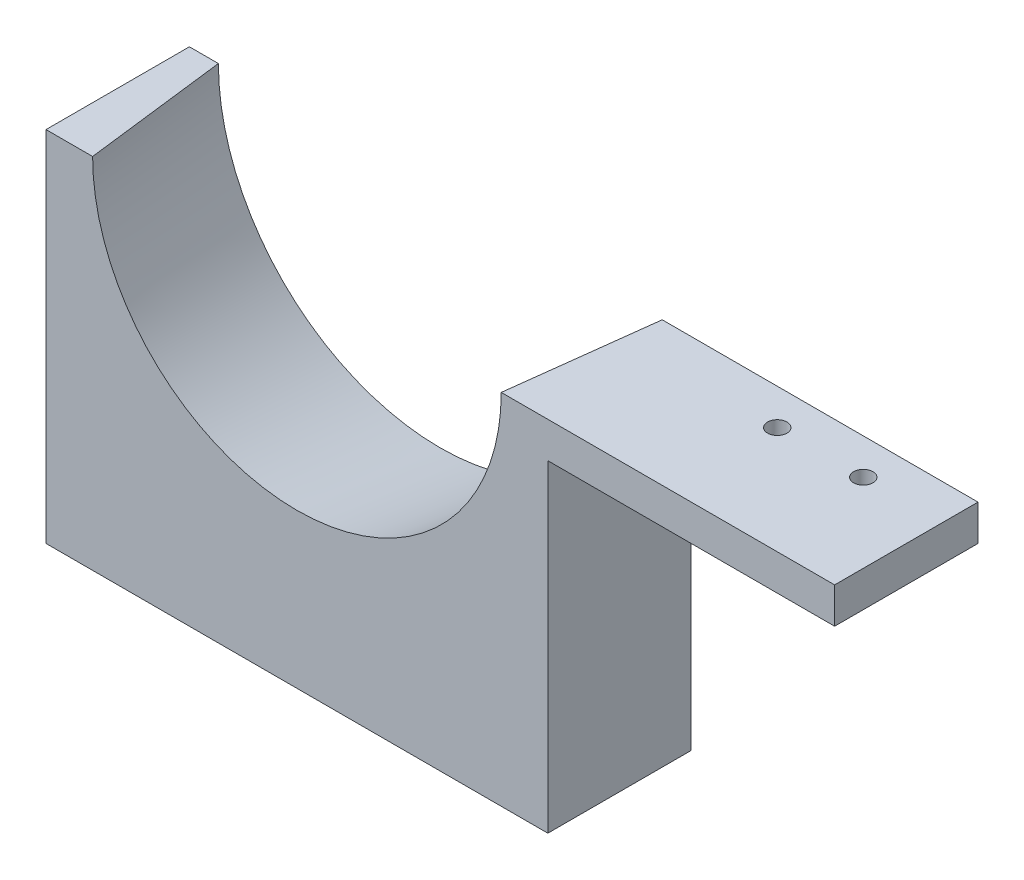
SolidWorks part; units mm, degrees
ref_plane "Front Plane" through (0, 0, 0) normal (0, 0, 1) x (1, 0, 0)
ref_plane "Top Plane" through (0, 0, 0) normal (0, 1, 0) x (1, 0, 0)
ref_plane "Right Plane" through (0, 0, 0) normal (1, 0, 0) x (0, 0, -1)
sketch "Sketch1" plane through (0, 0, 0) normal (0, 0, 1) x (1, 0, 0)
  line L1 (0, 0) -> (-40, 0)
  line L2 (0, 0) -> (0, -5)
  line L3 (0, -5) -> (-40, -5)
  line L4 (-40, 0) -> (-40, -5)
  line L5 (-40, 0) -> (-110, 0)
  line L6 (-40, 0) -> (-40, -50)
  line L7 (-40, -50) -> (-110, -50)
  line L8 (-110, 0) -> (-110, -50)
  dimension "D1" = 5
  dimension "D2" = 50
  dimension "D3" = 70
  dimension "D4" = 40
extrude "Boss-Extrude1" add sketch "Sketch1" along normal blind 20 contours L1 L4 L3 L2 | L5 L8 L7 L6 L4
sketch "Sketch2" plane through (0, 0, 20) normal (0, 0, 1) x (1, 0, 0)
  line L0 (0, 0) -> (-110, 0) construction
  line L1 (-40, -50) -> (-110, -50) construction
  circle A0 centre (-75, 0) radius 28.5
  point P4 (0, 0)
  point P7 (-75, -50)
  dimension "D1" = 57
extrude "Cut-Extrude1" cut sketch "Sketch2" against normal through all draft 7 draft outward yes
sketch "Sketch3" plane through (0, -5, 0) normal (0, -1, 0) x (1, 0, 0)
  circle A2 centre (-23, 5) radius 1.35
  circle A3 centre (-11, 5) radius 1.35
  dimension "D1" = 2.7
  dimension "D2" = 2.7
extrude "Cut-Extrude2" cut sketch "Sketch3" against normal through all
